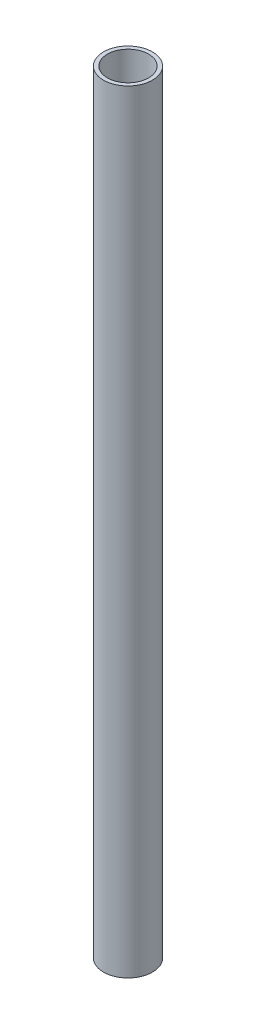
SolidWorks part; units mm, degrees
ref_plane "Front Plane" through (0, 0, 0) normal (0, 0, 1) x (1, 0, 0)
ref_plane "Top Plane" through (0, 0, 0) normal (0, 1, 0) x (1, 0, 0)
ref_plane "Right Plane" through (0, 0, 0) normal (1, 0, 0) x (0, 0, -1)
sketch "Sketch1" plane through (0, 0, 0) normal (0, 1, 0) x (1, 0, 0)
  circle A0 centre (0, 0) radius 24.13
  circle A1 centre (0, 0) radius 20.32
  dimension "D1" = 48.26
  dimension "D2" = 40.64
extrude "Boss-Extrude1" add sketch "Sketch1" along normal blind 761.0475
